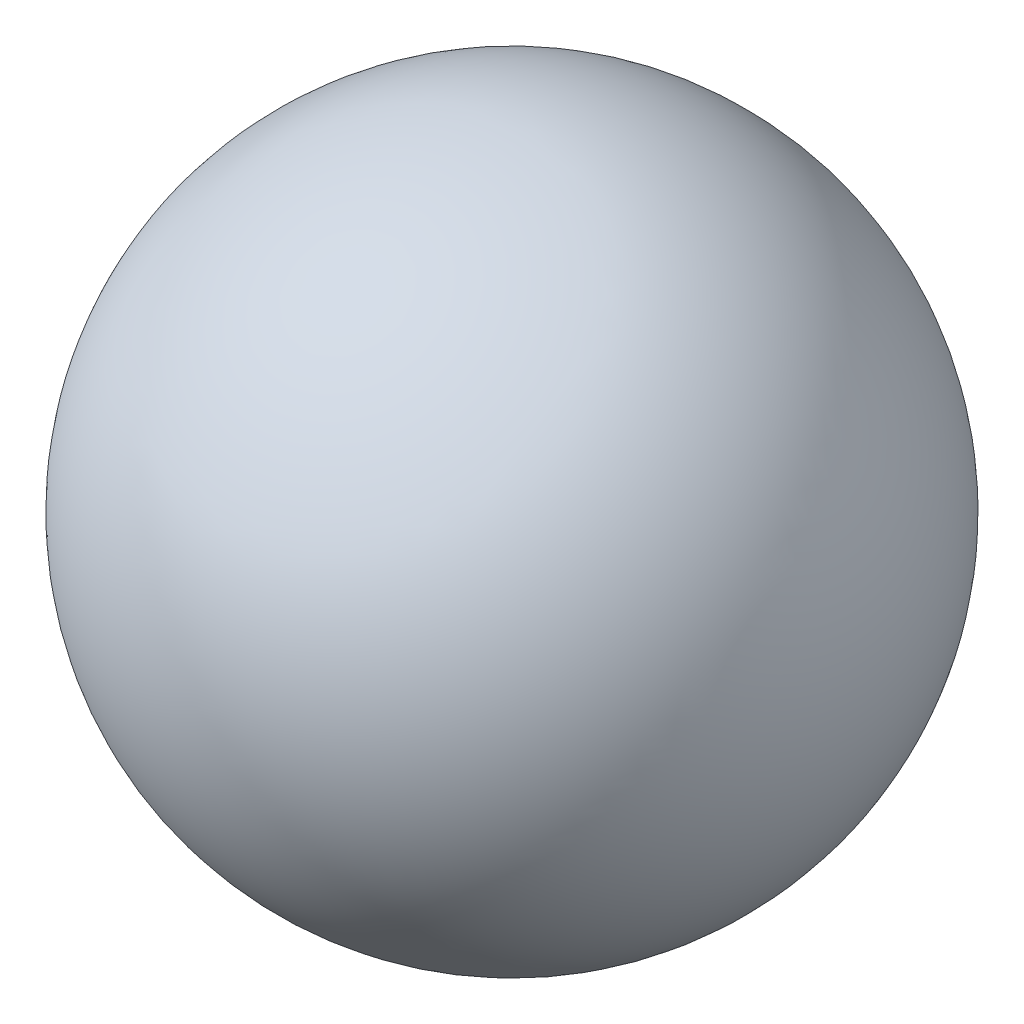
SolidWorks part; units mm, degrees
ref_plane "Front" through (0, 0, 0) normal (0, 0, 1) x (1, 0, 0)
ref_plane "Top" through (0, 0, 0) normal (0, 1, 0) x (1, 0, 0)
ref_plane "Right" through (0, 0, 0) normal (1, 0, 0) x (0, 0, -1)
sketch "Sketch1" plane through (0, 0, 0) normal (0, 0, 1) x (1, 0, 0)
  line L0 (-0.22, 0) -> (0.22, 0)
  arc A0 (0.22, 0) -> (-0.22, 0) centre (0, 0) cw
  dimension "D1" = 0.22
revolve "Revolve1" add sketch "Sketch1" angle 360 about L0
